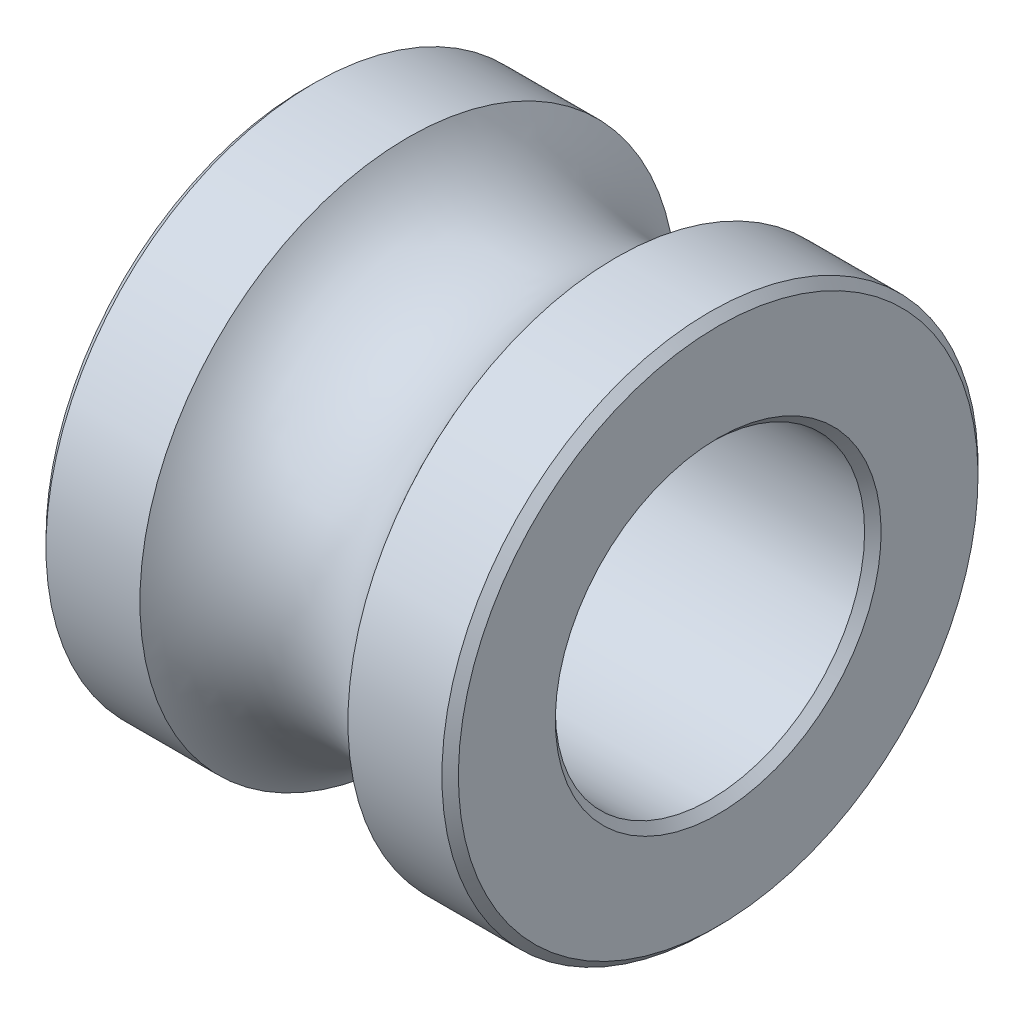
SolidWorks part; units mm, degrees
ref_plane "Front" through (0, 0, 0) normal (0, 0, 1) x (1, 0, 0)
ref_plane "Top" through (0, 0, 0) normal (0, 1, 0) x (1, 0, 0)
ref_plane "Right" through (0, 0, 0) normal (1, 0, 0) x (0, 0, -1)
sketch "Sketch1" plane through (0, 0, 0) normal (0, 0, 1) x (1, 0, 0)
  line L0 (-6.429, 0) -> (6.429, 0) construction
  line L1 (-2, -1.5) -> (2, -1.5) construction
  line L2 (-1.6, -4) -> (-0.9367, -4) construction
  line L3 (-2, -4) -> (-2, -5) construction
  line L4 (-2, -5) -> (2, -5) construction
  line L5 (2, -4) -> (2, -5) construction
  line L6 (0, -1.5) -> (0, -5) construction
  line L7 (-2, -2.6) -> (2, -2.6) construction
  line L8 (-1.6, -4) -> (-1.6, -4.1) construction
  line L9 (-1.6, -4.1) -> (-1.8, -4.1) construction
  line L10 (-1.8, -4.1) -> (-1.8, -4) construction
  line L11 (-1.8, -4) -> (-2, -4) construction
  line L12 (1.8, -4) -> (2, -4) construction
  line L13 (1.8, -4.1) -> (1.8, -4) construction
  line L14 (1.6, -4.1) -> (1.8, -4.1) construction
  line L15 (1.6, -4) -> (1.6, -4.1) construction
  line L16 (0.9367, -4) -> (1.6, -4) construction
  line L17 (-2, -1.5) -> (-2, -2.6)
  line L18 (-2, -2.6) -> (-1.0087, -2.6)
  line L19 (-2, -1.5) -> (2, -1.5)
  line L20 (2, -1.5) -> (2, -2.6)
  line L21 (2, -2.6) -> (1.0087, -2.6)
  circle A0 centre (0, -3.25) radius 1.2 construction
  arc A1 (-1.0087, -2.6) -> (1.0087, -2.6) centre (0, -3.25) cw
  point P13 (0, -3.25)
  point P15 (-1.8, -4.05)
  point P26 (0, 0)
  point P30 (0, -2.6)
  dimension "D3" = 2.4
  dimension "D1" = 5
  dimension "D2" = 1.5
  dimension "D4" = 2.6
  dimension "D5" = 4
  dimension "D6" = 0.4
  dimension "D7" = 4
  dimension "D8" = 0.1
  dimension "D9" = 0.2
  dimension "D11" = 4
revolve "Revolve1" add sketch "Sketch1" angle 360 about L0
chamfer "Chamfer1" distance 0.08 angle 45 4 edges at (-2, -1.5, 0) (-2, -2.6, 0) (2, -2.6, 0) (2, -1.5, 0)
